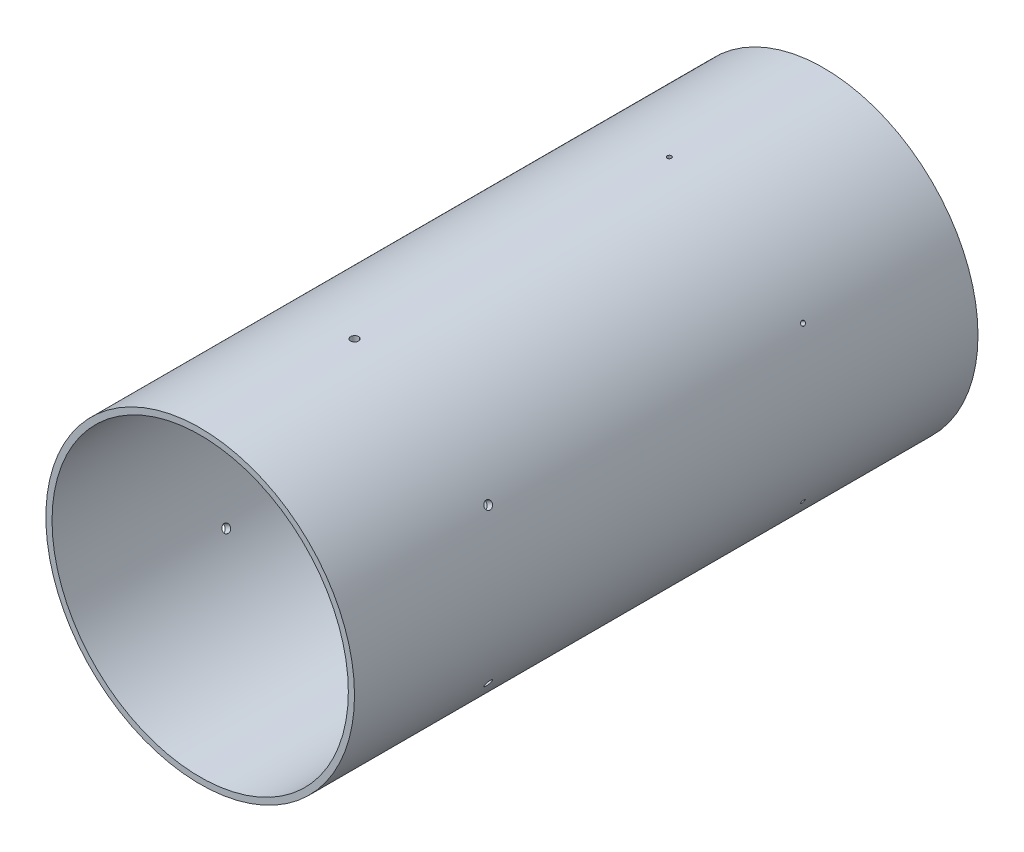
SolidWorks part; units mm, degrees
ref_plane "Front Plane" through (0, 0, 0) normal (0, 0, 1) x (1, 0, 0)
ref_plane "Top Plane" through (0, 0, 0) normal (0, 1, 0) x (1, 0, 0)
ref_plane "Right Plane" through (0, 0, 0) normal (1, 0, 0) x (0, 0, -1)
sketch "Sketch1" plane through (0, 0, 0) normal (0, 0, 1) x (1, 0, 0)
  circle A0 centre (0, 0) radius 79.375
  circle A1 centre (0, 0) radius 76.2
  dimension "D1" = 158.75
  dimension "D2" = 3.175
extrude "Boss-Extrude1" add sketch "Sketch1" along normal blind 320.675
ref_plane "Plane1" through (0, 79.375, 0) normal (0, 1, 0) x (1, 0, 0)
sketch "Sketch2" plane through (0, 79.375, 0) normal (0, 1, 0) x (1, 0, 0)
  line L0 (79.375, 0) -> (-79.375, 0) construction
  point P0 (0, -79.375)
  dimension "D1" = 79.375
hole_wizard "#4-40 Tapped Hole1" positions "Sketch5" profile "Sketch6" tap size "#4-40" standard "ANSI Inch"
sketch "Sketch5" plane through (0, 79.375, 0) normal (0, 1, 0) x (1, 0, 0)
  point P0 (0, -79.375)
sketch "Sketch6" plane through (0, 79.375, 79.375) normal (1, 0, 0) x (0, 0, 1)
  line L0 (0, 0) -> (0, 3.175)
  line L1 (0, 3.175) -> (1.1303, 3.175)
  line L2 (1.1303, 3.175) -> (1.1303, 0)
  line L5 (1.1303, 0) -> (0, 0)
  line L11 (0, -6.35) -> (0, 107.95) construction
  dimension "Thru Tap Drill Dia." = 2.2606
  dimension "Thru Tap Drill Depth" = 3.175
cosmetic thread "Hole Thread1" parameters "D2"=2.8448
sketch "Sketch7" plane through (0, 79.375, 0) normal (0, 1, 0) x (1, 0, 0)
  line L0 (-79.375, -320.675) -> (79.375, -320.675) construction
  point P0 (0, -241.3)
  dimension "D1" = 79.375
hole_wizard "#10-32 Tapped Hole1" positions "Sketch8" profile "Sketch9" tap size "#10-32" standard "ANSI Inch"
sketch "Sketch8" plane through (0, 79.375, 0) normal (0, 1, 0) x (1, 0, 0)
  point P0 (0, -241.3)
sketch "Sketch9" plane through (0, 79.375, 241.3) normal (1, 0, 0) x (0, 0, 1)
  line L0 (0, 0) -> (0, 3.175)
  line L1 (0, 3.175) -> (2.0193, 3.175)
  line L2 (2.0193, 3.175) -> (2.0193, 0)
  line L5 (2.0193, 0) -> (0, 0)
  line L11 (0, -6.35) -> (0, 107.95) construction
  dimension "Thru Tap Drill Dia." = 4.0386
  dimension "Thru Tap Drill Depth" = 3.175
cosmetic thread "Hole Thread2" parameters "D2"=4.826
pattern_circular "CirPattern1" count 6 over 360 about axis through (0, 0, 320.675) along (0, 0, 1) of "#4-40 Tapped Hole1", "#10-32 Tapped Hole1"
cosmetic thread "Hole Thread3" parameters "D2"=2.8448
cosmetic thread "Hole Thread4" parameters "D2"=2.8448
cosmetic thread "Hole Thread5" parameters "D2"=2.8448
cosmetic thread "Hole Thread6" parameters "D2"=4.826
cosmetic thread "Hole Thread7" parameters "D2"=4.826
cosmetic thread "Hole Thread8" parameters "D2"=4.826
cosmetic thread "Hole Thread9" parameters "D2"=2.8448
cosmetic thread "Hole Thread10" parameters "D2"=2.8448
cosmetic thread "Hole Thread11" parameters "D2"=4.826
cosmetic thread "Hole Thread12" parameters "D2"=4.826
